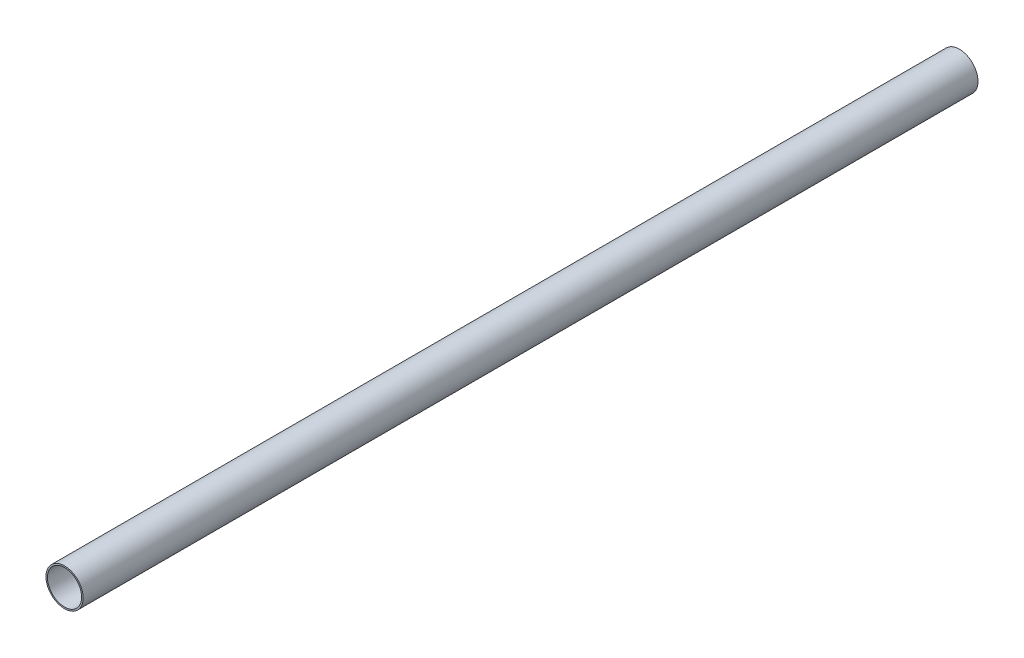
SolidWorks part; units mm, degrees
ref_plane "Front Plane" through (0, 0, 0) normal (0, 0, 1) x (1, 0, 0)
ref_plane "Top Plane" through (0, 0, 0) normal (0, 1, 0) x (1, 0, 0)
ref_plane "Right Plane" through (0, 0, 0) normal (1, 0, 0) x (0, 0, -1)
sketch "Sketch1" plane through (0, 0, 0) normal (0, 0, 1) x (1, 0, 0)
  line L0 (13.716, 0) -> (12.6238, 0) construction
  circle A0 centre (0, 0) radius 13.716
  circle A1 centre (0, 0) radius 12.6238 construction
  dimension "Dia." = 27.432
  dimension "Wall Thick." = 1.0922
extrude "Extrude-Thin1" add sketch "Sketch1" along normal mid plane 660.4 thin thin type one direction reverse wall 1.0922
equation "\"D5@Extrude-Thin1\" = \"Wall Thick.@Sketch1\""
